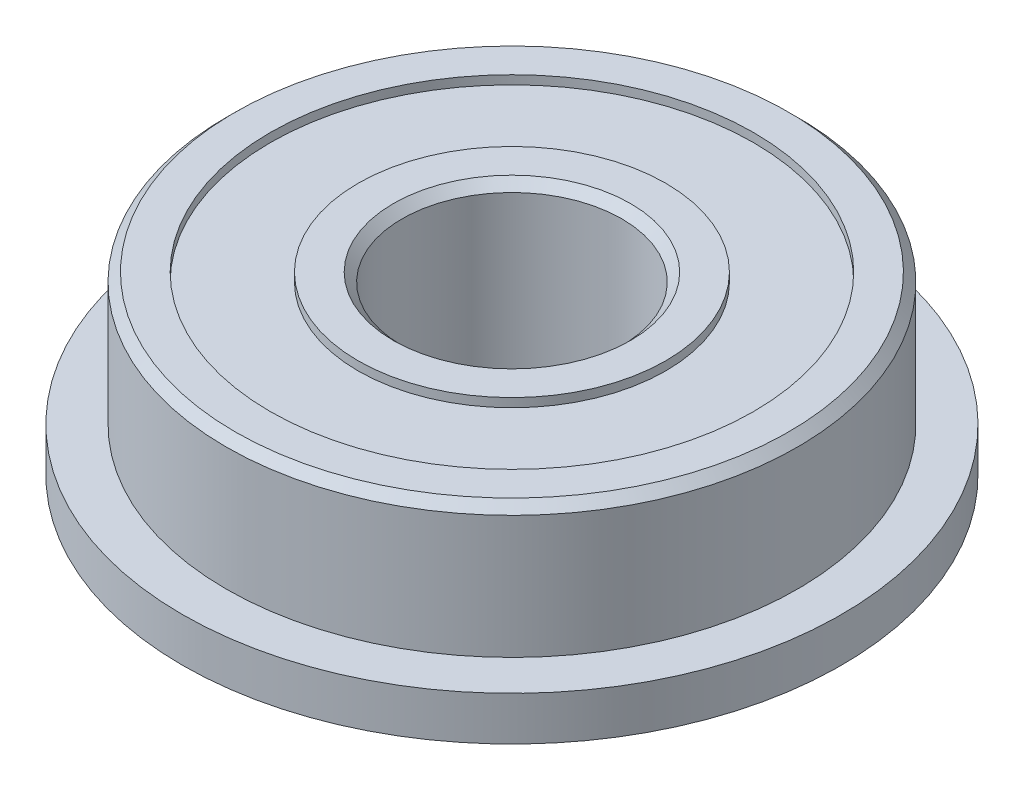
SolidWorks part; units mm, degrees
ref_plane "Front Plane" through (0, 0, 0) normal (0, 0, 1) x (1, 0, 0)
ref_plane "Top Plane" through (0, 0, 0) normal (0, 1, 0) x (1, 0, 0)
ref_plane "Right Plane" through (0, 0, 0) normal (1, 0, 0) x (0, 0, -1)
sketch "Sketch2" plane through (0, 0, 0) normal (0, 0, 1) x (1, 0, 0)
  line L0 (-2.5, 0) -> (0, 0) construction
  line L1 (-6.5, 4) -> (-2.5, 4)
  line L2 (-6.5, 4) -> (-6.5, 1)
  line L4 (-2.5, 4) -> (-2.5, 0)
  line L5 (-6.5, 1) -> (-7.5, 1)
  line L7 (-2.5, 0) -> (-7.5, 0)
  line L8 (-7.5, 1) -> (-7.5, 0)
  line L9 (0, 1.9216) -> (0, -1.6319) construction
  dimension "D1" = 4
  dimension "D2" = 1
  dimension "D3" = 7.5
  dimension "D4" = 6.5
  dimension "D5" = 2.5
revolve "Revolve1" add sketch "Sketch2" angle 360 about L9
sketch "Sketch3" plane through (0, 4, 0) normal (0, 1, 0) x (1, 0, 0)
  circle A0 centre (0, 0) radius 3.5
  circle A3 centre (0, 0) radius 5.5
  circle A4 centre (0, 0) radius 6.5 construction
  point P5 (0, -0.0767)
  dimension "D1" = 7
  dimension "D2" = 1
extrude "Cut-Extrude1" cut sketch "Sketch3" against normal blind 0.2
ref_plane "Plane1" through (0, 2, 0) normal (0, 1, 0) x (1, 0, 0)
mirror "Mirror1" about plane through (0, 2, 0) normal (0, 1, 0) of "Cut-Extrude1"
chamfer "Chamfer1" distance 0.2 angle 45 3 edges at (0, 4, 6.5) (0, 0, 2.5) (0, 4, 2.5)
